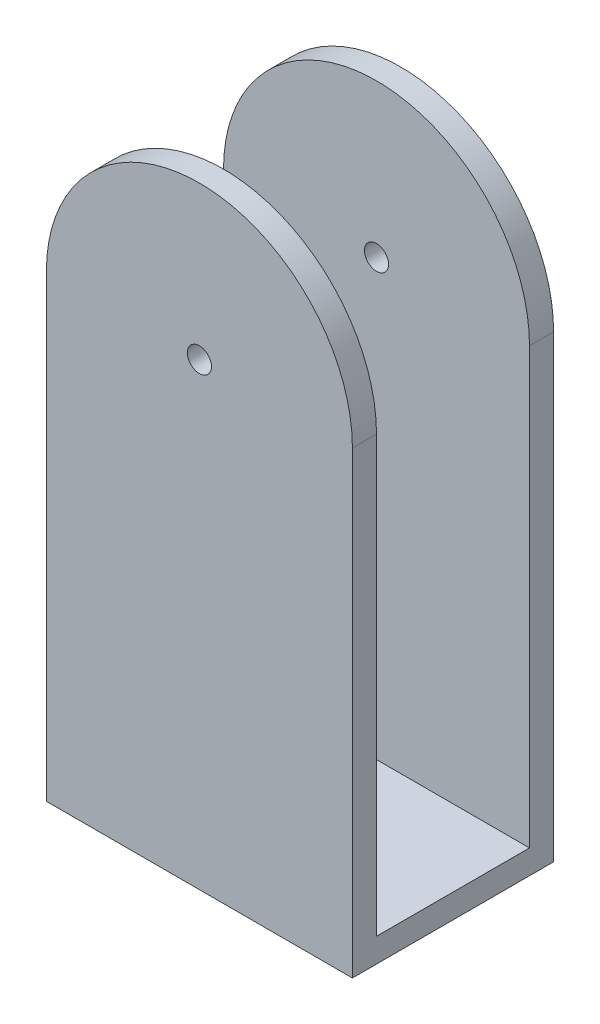
SolidWorks part; units mm, degrees
ref_plane "Front Plane" through (0, 0, 0) normal (0, 0, 1) x (1, 0, 0)
ref_plane "Top Plane" through (0, 0, 0) normal (0, 1, 0) x (1, 0, 0)
ref_plane "Right Plane" through (0, 0, 0) normal (1, 0, 0) x (0, 0, -1)
sketch "Sketch1" plane through (0, 0, 0) normal (0, 0, 1) x (1, 0, 0)
  line L0 (0, 0) -> (0, 19.05)
  line L1 (12.7, 19.05) -> (12.7, 0)
  line L2 (12.7, 0) -> (0, 0)
  arc A0 (0, 19.05) -> (12.7, 19.05) centre (6.35, 19.05) cw
  circle A1 centre (6.35, 19.05) radius 0.5
  dimension "D3" = 1
  dimension "D1" = 12.7
  dimension "D2" = 19.05
extrude "Boss-Extrude1" add sketch "Sketch1" along normal blind 1
sketch "Sketch2" plane through (0, 0, 1) normal (0, 0, 1) x (1, 0, 0)
  line L0 (12.7, 0) -> (12.7, 19.05) construction
  line L1 (0, 0) -> (12.7, 0)
  line L2 (0, 0) -> (0, 1)
  line L3 (0, 1) -> (12.7, 1)
  line L4 (12.7, 0) -> (12.7, 1)
  dimension "D1" = 1
extrude "Boss-Extrude2" add sketch "Sketch2" along normal blind 6.35
sketch "Sketch3" plane through (0, 0, 7.35) normal (0, 0, 1) x (1, 0, 0)
  line L3 (0, 0) -> (12.7, 0)
  line L4 (0, 19.05) -> (0, 0)
  line L5 (12.7, 0) -> (12.7, 19.05)
  line L6 (0, 0) -> (12.7, 0)
  line L7 (0, 19.05) -> (0, 0)
  line L8 (12.7, 0) -> (12.7, 19.05)
  circle A0 centre (6.35, 19.05) radius 0.5 construction
  arc A1 (12.7, 19.05) -> (0, 19.05) centre (6.35, 19.05) ccw
  arc A2 (12.7, 19.05) -> (0, 19.05) centre (6.35, 19.05) ccw
  circle A3 centre (6.35, 19.05) radius 0.5
  dimension "D1" = 0
extrude "Boss-Extrude3" add sketch "Sketch3" along normal blind 1
sketch "Sketch4" plane through (0, 0, 0) normal (0, -1, 0) x (1, 0, 0)
  line L0 (12.7, 4.175) -> (0, 4.175) construction
  line L1 (12.7, 8.35) -> (12.7, 0) construction
  line L2 (0, 8.35) -> (0, 0) construction
